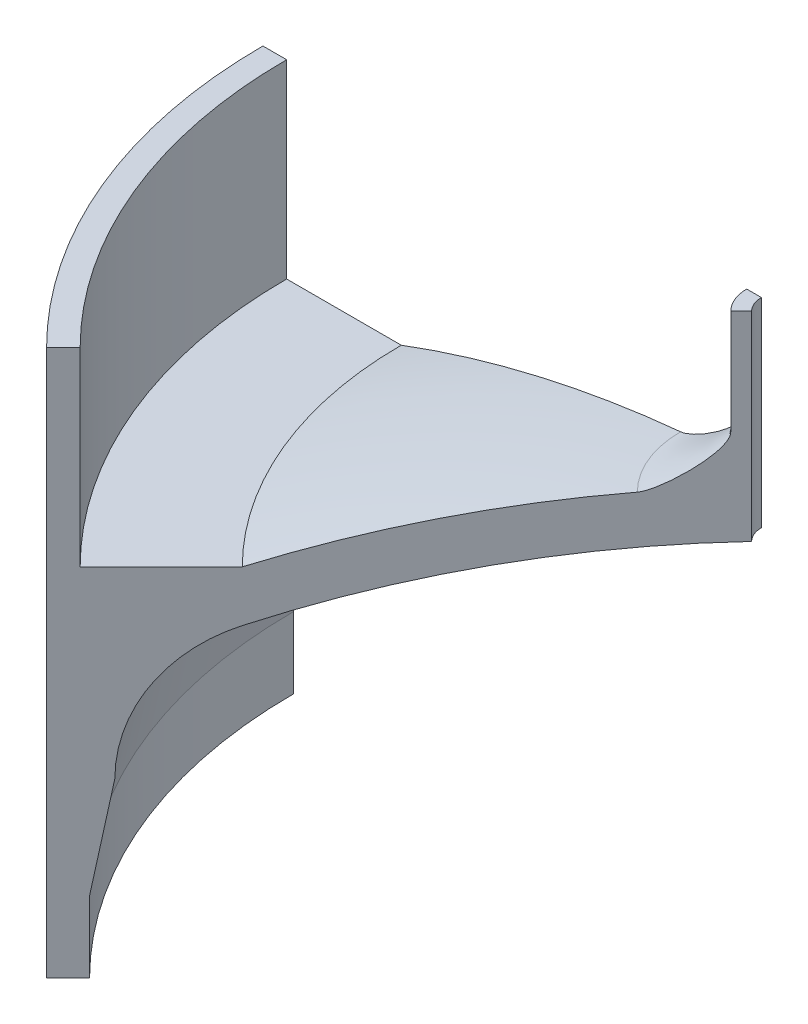
SolidWorks part; units mm, degrees
material "6061-T6 (SS)"
ref_plane "Front Plane" through (0, 0, 0) normal (0, 0, 1) x (1, 0, 0)
ref_plane "Top Plane" through (0, 0, 0) normal (0, 1, 0) x (1, 0, 0)
ref_plane "Right Plane" through (0, 0, 0) normal (1, 0, 0) x (0, 0, -1)
ref_axis "Axis1" through (0, 127.061, 0) along (0, -1, 0)
sketch "Sketch1" plane through (0, 0, 0) normal (0, 0, 1) x (1, 0, 0)
  line L0 (-69.85, 10.9548) -> (-69.85, 73.025)
  line L2 (0, 127.061) -> (0, -81.9141) construction
  line L3 (-69.85, 10.9548) -> (-69.85, 0)
  line L5 (-67.3735, 0) -> (-65.786, 0)
  line L6 (55, 0) -> (-55, 0) construction
  line L7 (-66.675, 73.025) -> (-69.85, 73.025)
  line L9 (-66.675, 47.625) -> (-51.3431, 47.625)
  line L10 (-69.85, 0) -> (-67.3735, 0)
  line L11 (-66.675, 47.625) -> (-66.675, 73.025)
  line L12 (-5.1435, 63.2611) -> (-5.1435, 77.2311)
  line L13 (-5.1435, 77.2311) -> (-3.175, 77.2311)
  line L14 (-3.175, 77.2311) -> (-3.175, 50.5611)
  line L15 (-65.786, 0) -> (-65.786, 9.525)
  line L16 (-65.786, 9.525) -> (-63.3918, 23.1034)
  arc A0 (-63.3918, 23.1034) -> (-51.3431, 40.8202) centre (-44.3418, 23.1034) cw
  arc A1 (-51.3431, 40.8202) -> (-3.175, 50.5611) centre (0, -89.1028) cw
  arc A3 (-51.3431, 47.625) -> (-13.9848, 56.2761) centre (0, -89.1028) cw
  spline S0 degree 3 poles (-5.1435, 63.2611) (-5.1435, 60.9924) (-11.7914, 56.4871) (-13.9848, 56.2761) knots 0 0 0 0 1 1 1 1
  point P14 (-66.5798, 0)
  dimension "D5" = 19.05
  dimension "D6" = 139.7
  dimension "D7" = 146.05
  dimension "D8" = 10.9548
  dimension "D2" = 170
  dimension "D3" = 62.0702
  dimension "D4" = 1.5875
  dimension "D9" = 25.4
  dimension "D10" = 3.175
  dimension "D11" = 5.1435
  dimension "D12" = 6.985
  dimension "D13" = 13.97
  dimension "D14" = 3.175
  dimension "D15" = 4.064
  dimension "D16" = 69.85
  dimension "D17" = 13.5784
  dimension "D18" = 12.7
revolve "Revolve2" add sketch "Sketch1" angle 360 about axis through (0, 127.061, 0) along (0, -1, 0)
sketch "Sketch2" plane through (0, 0, 0) normal (0, 0, 1) x (1, 0, 0)
  line L0 (0, 127.061) -> (0, -81.9141) construction
  line L1 (0, 87.1374) -> (-97.8719, 87.1374)
  line L2 (0, 87.1374) -> (0, -26.2798)
  line L3 (0, -26.2798) -> (-97.8719, -26.2798)
  line L4 (-97.8719, 87.1374) -> (-97.8719, -26.2798)
revolve "Cut-Revolve1" cut sketch "Sketch2" angle 315 about axis through (0, 127.061, 0) along (0, -1, 0)
